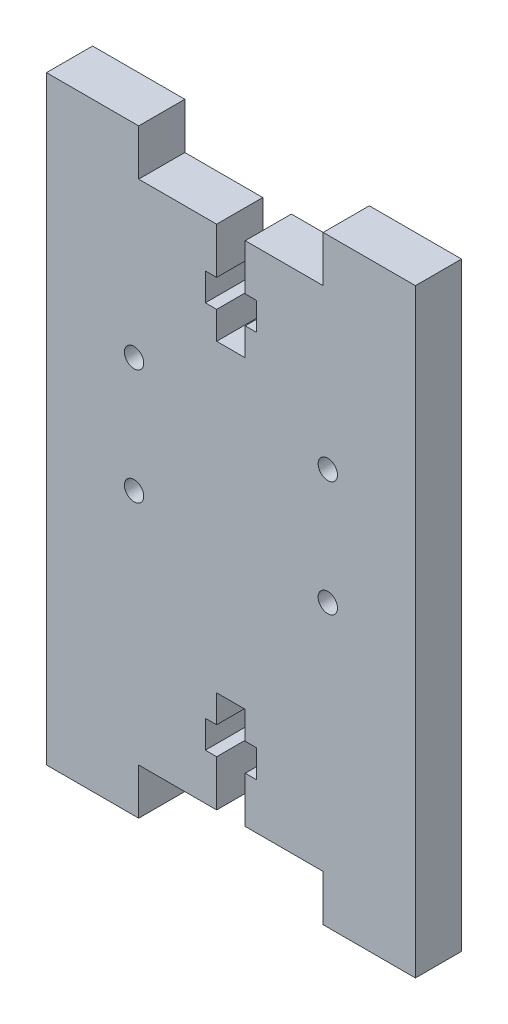
SolidWorks part; units mm, degrees
ref_plane "Plan de face" through (0, 0, 0) normal (0, 0, 1) x (1, 0, 0)
ref_plane "Plan de dessus" through (0, 0, 0) normal (0, 1, 0) x (1, 0, 0)
ref_plane "Plan de droite" through (0, 0, 0) normal (1, 0, 0) x (0, 0, -1)
ref_plane "Plan1" through (0, 0, 5) normal (0, 0, 1) x (1, 0, 0)
sketch "Esquisse1" plane through (0, 0, 5) normal (0, 0, 1) x (1, 0, 0)
  line L0 (20, 31) -> (-20, 31)
  line L1 (-20, 31) -> (-20, -31)
  line L2 (-20, -31) -> (20, -31)
  line L3 (20, -31) -> (20, 31)
extrude "Boss.-Extru.1" add sketch "Esquisse1" against normal blind 5
sketch "Esquisse2" plane through (0, 0, 0) normal (0, 0, -1) x (-1, 0, 0)
  line L0 (10, 31) -> (-10, 31)
  line L1 (-10, 31) -> (-10, 27.5)
  line L2 (-10, 27.5) -> (10, 27.5)
  line L3 (10, 27.5) -> (10, 31)
extrude "Enlèv. mat.-Extru.1" cut sketch "Esquisse2" against normal through all
sketch "Esquisse3" plane through (0, 0, 0) normal (0, 0, -1) x (-1, 0, 0)
  line L0 (-10, -31) -> (10, -31)
  line L1 (10, -31) -> (10, -27.5)
  line L2 (10, -27.5) -> (-10, -27.5)
  line L3 (-10, -27.5) -> (-10, -31)
extrude "Enlèv. mat.-Extru.2" cut sketch "Esquisse3" against normal through all
sketch "Esquisse8" plane through (0, 0, 5) normal (0, 0, 1) x (1, 0, 0)
  line L8 (-10, -27.5) -> (10, -27.5) construction
  line L9 (-1.55, -27.5) -> (1.55, -27.5)
  line L10 (-1.55, -27.5) -> (-1.55, -16.5)
  line L11 (-1.55, -16.5) -> (1.55, -16.5)
  line L12 (1.55, -27.5) -> (1.55, -16.5)
  line L13 (0, 0) -> (11.7651, 0) construction
  line L14 (-2.775, -19.5) -> (2.775, -19.5)
  line L15 (-2.775, -19.5) -> (-2.775, -22.5)
  line L16 (-2.775, -22.5) -> (2.775, -22.5)
  line L17 (2.775, -19.5) -> (2.775, -22.5)
  line L18 (2.775, 19.5) -> (2.775, 22.5)
  line L19 (-2.775, 22.5) -> (2.775, 22.5)
  line L20 (-2.775, 19.5) -> (-2.775, 22.5)
  line L21 (-2.775, 19.5) -> (2.775, 19.5)
  line L22 (1.55, 27.5) -> (1.55, 16.5)
  line L23 (-1.55, 16.5) -> (1.55, 16.5)
  line L24 (-1.55, 27.5) -> (-1.55, 16.5)
  line L25 (-1.55, 27.5) -> (1.55, 27.5)
  line L27 (10, -27.5) -> (10, -31) construction
  line M13 (10, 27.5) -> (-10, 27.5)
  line M19 (-10, -27.5) -> (10, -27.5)
  dimension "D1" = 3.1
  dimension "D2" = 5
  dimension "D3" = 3
  dimension "D4" = 3
  dimension "D5" = 5.55
  dimension "D6" = 1.225
  dimension "D7" = 8.45
extrude "Enlèv. mat.-Extru.3" cut sketch "Esquisse8" against normal through all contours L19 L24 L21 L22 | L24 L19 L22 M13 | L24 L19 L20 L21 | L19 L22 L21 L18 | L21 L24 L23 L22 | L10 L14 L12 L11 | L15 L16 L10 L14 | L10 L16 L12 L14 | L17 L14 L12 L16 | L16 L10 L12 M19
sketch "Esquisse9" plane through (0, 0, 5) normal (0, 0, 1) x (1, 0, 0)
  line L0 (-20, 31) -> (-20, -31) construction
  line L1 (-20, 32.5) -> (-10, 32.5)
  line L2 (-20, 32.5) -> (-20, -32.5)
  line L3 (-20, -32.5) -> (-10, -32.5)
  line L4 (-10, 32.5) -> (-10, -32.5)
  line L5 (20, 32.5) -> (10, 32.5)
  line L6 (20, 32.5) -> (20, -32.5)
  line L7 (20, -32.5) -> (10, -32.5)
  line L8 (10, 32.5) -> (10, -32.5)
  line L9 (-10, 27.5) -> (-10, 31) construction
  line L10 (-1.55, 27.5) -> (-10, 27.5) construction
  line L11 (-10, -27.5) -> (-1.55, -27.5) construction
  line L12 (1.55, -27.5) -> (10, -27.5) construction
  line L13 (20, -31) -> (20, 31) construction
  line L15 (10, 27.5) -> (1.55, 27.5) construction
  line L16 (10, 31) -> (10, 27.5) construction
  dimension "D1" = 0
  dimension "D2" = 0
  dimension "D3" = 5
  dimension "D4" = 5
  dimension "D5" = 5
  dimension "D6" = 0
  dimension "D7" = 5
  dimension "D8" = 0
extrude "Boss.-Extru.2" add sketch "Esquisse9" against normal blind 5
sketch "Esquisse10" plane through (0, 0, 0) normal (0, 0, -1) x (-1, 0, 0)
  circle A0 centre (-10.5, 10.5) radius 1.05
  circle A1 centre (10.5, 10.5) radius 1.05
  circle A2 centre (10.5, -2) radius 1.05
  circle A3 centre (-10.5, -2) radius 1.05
  dimension "D1" = 2.1
  dimension "D2" = 10.5
  dimension "D5" = 10.5
  dimension "D3" = 2
  dimension "D4" = 2
extrude "Enlèv. mat.-Extru.4" cut sketch "Esquisse10" against normal through all
